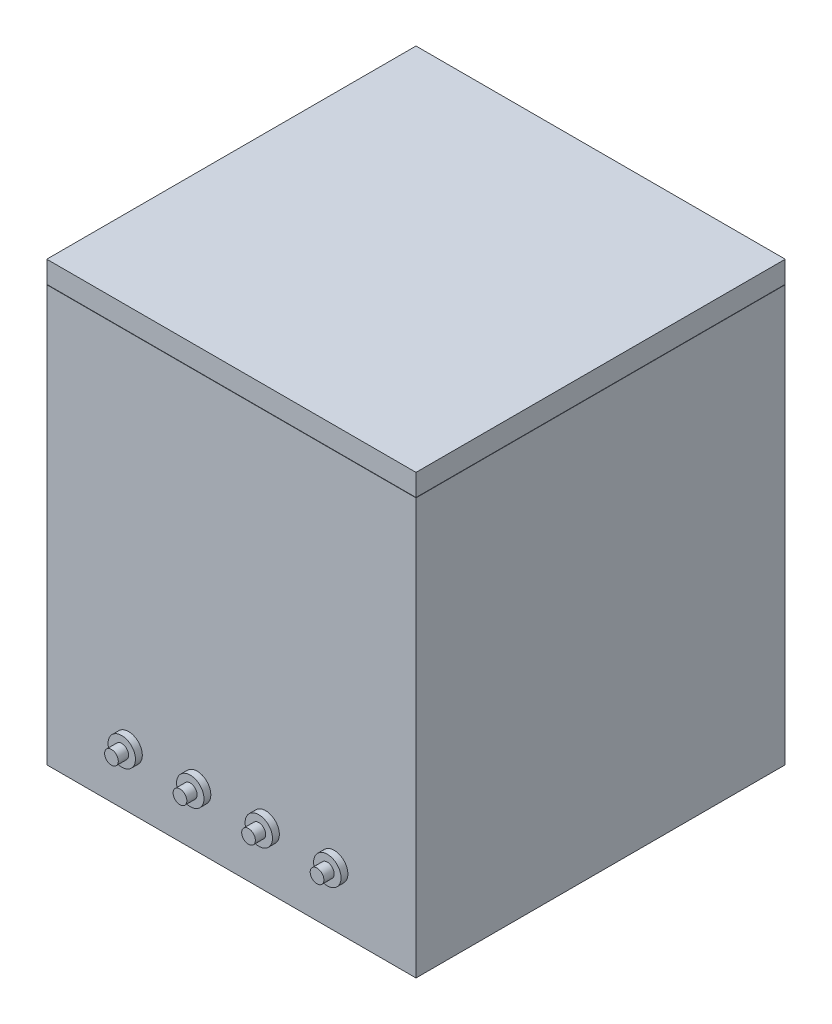
SolidWorks part; units mm, degrees
ref_plane "Front Plane" through (0, 0, 0) normal (0, 0, 1) x (1, 0, 0)
ref_plane "Top Plane" through (0, 0, 0) normal (0, 1, 0) x (1, 0, 0)
ref_plane "Right Plane" through (0, 0, 0) normal (1, 0, 0) x (0, 0, -1)
sketch "Sketch1" plane through (0, 0, 0) normal (0, 1, 0) x (1, 0, 0)
  line L1 (-47.5315, 47.5315) -> (47.5315, 47.5315)
  line L2 (-47.5315, 47.5315) -> (-47.5315, -47.5315)
  line L3 (-47.5315, -47.5315) -> (47.5315, -47.5315)
  line L4 (47.5315, 47.5315) -> (47.5315, -47.5315)
  line L5 (-47.5315, 47.5315) -> (47.5315, -47.5315) construction
  line L6 (-47.5315, -47.5315) -> (47.5315, 47.5315) construction
  line L7 (-53.8815, 53.8815) -> (53.8815, 53.8815)
  line L8 (-53.8815, 53.8815) -> (-53.8815, -53.8815)
  line L9 (-53.8815, -53.8815) -> (53.8815, -53.8815)
  line L10 (53.8815, 53.8815) -> (53.8815, -53.8815)
  line L11 (-53.8815, 53.8815) -> (53.8815, -53.8815) construction
  line L12 (-53.8815, -53.8815) -> (53.8815, 53.8815) construction
  circle A0 centre (0, 0) radius 76.2 construction
  point P0 (0, 0)
  dimension "D1" = 152.4
  dimension "D2" = 6.35
  dimension "D3" = 95.0631
extrude "Boss-Extrude1" add sketch "Sketch1" along normal blind 115
sketch "Sketch2" plane through (0, 0, 0) normal (0, -1, 0) x (1, 0, 0)
  line L1 (-53.8815, 53.8815) -> (53.8815, 53.8815)
  line L2 (-53.8815, 53.8815) -> (-53.8815, -53.8815)
  line L3 (-53.8815, -53.8815) -> (53.8815, -53.8815)
  line L4 (53.8815, 53.8815) -> (53.8815, -53.8815)
  line L5 (-53.8815, 53.8815) -> (53.8815, -53.8815) construction
  line L6 (-53.8815, -53.8815) -> (53.8815, 53.8815) construction
  point P0 (0, 0)
extrude "Boss-Extrude2" add sketch "Sketch2" along normal blind 6.35
ref_plane "Plane1" through (0, 115.1, 0) normal (0, 1, 0) x (1, 0, 0)
sketch "Sketch3" plane through (0, 115.1, 0) normal (0, 1, 0) x (1, 0, 0)
  line L1 (-53.8815, 53.8815) -> (53.8815, 53.8815)
  line L2 (-53.8815, 53.8815) -> (-53.8815, -53.8815)
  line L3 (-53.8815, -53.8815) -> (53.8815, -53.8815)
  line L4 (53.8815, 53.8815) -> (53.8815, -53.8815)
  line L5 (-53.8815, 53.8815) -> (53.8815, -53.8815) construction
  line L6 (-53.8815, -53.8815) -> (53.8815, 53.8815) construction
  point P0 (0, 0)
extrude "Boss-Extrude3" add sketch "Sketch3" along normal blind 6.35 separate body
sketch "Sketch4" plane through (0, -6.35, 0) normal (0, -1, 0) x (1, 0, 0)
  line L0 (0, 0) -> (0, -25) construction
  line L1 (0, -25) -> (-20, -25) construction
  line L2 (0, -25) -> (20, -25) construction
  circle A0 centre (-20, -25) radius 2.5
  circle A1 centre (20, -25) radius 2.5
  dimension "D2" = 5
  dimension "D1" = 40
  dimension "D3" = 25
extrude "Cut-Extrude1" cut sketch "Sketch4" against normal mid plane 6.35
ref_plane "Plane2" through (0, 10, 0) normal (0, 1, 0) x (1, 0, 0)
sketch "Sketch6" plane through (0, 10, 0) normal (0, 1, 0) x (1, 0, 0)
  line L0 (0, 0) -> (0, -53.8815) construction
  line L1 (-53.8815, -53.8815) -> (53.8815, -53.8815) construction
  line L2 (0, -53.8815) -> (-30, -53.8815) construction
  line L3 (-30, -53.8815) -> (-30, -58.8815)
  line L4 (-30, -58.8815) -> (-32, -58.8815)
  line L5 (-32, -58.8815) -> (-32, -55.8815)
  line L6 (-32, -55.8815) -> (-34, -55.8815)
  line L7 (-34, -55.8815) -> (-34, -53.8815)
  line L8 (-34, -53.8815) -> (-30, -53.8815)
  dimension "D1" = 30
  dimension "D2" = 5
  dimension "D3" = 2
  dimension "D4" = 4
  dimension "D5" = 2
revolve "Revolve1" add sketch "Sketch6" angle 360 about L3
pattern_linear "LPattern1" count 4 spacing 20 along (1, 0, 0) of "Revolve1"
